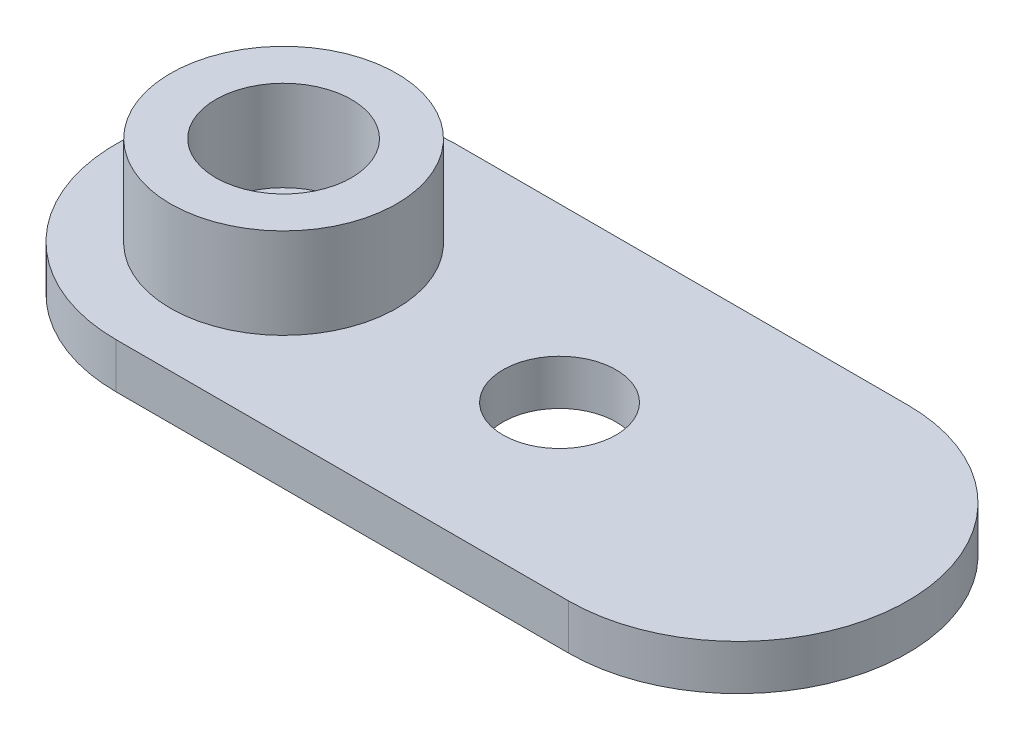
SolidWorks part; units mm, degrees
ref_plane "Front Plane" through (0, 0, 0) normal (0, 0, 1) x (1, 0, 0)
ref_plane "Top Plane" through (0, 0, 0) normal (0, 1, 0) x (1, 0, 0)
ref_plane "Right Plane" through (0, 0, 0) normal (1, 0, 0) x (0, 0, -1)
sketch "Sketch1" plane through (0, 0, 0) normal (0, 1, 0) x (1, 0, 0)
  line L0 (-7.5, 0.0986) -> (20, 0.0986) construction
  line L5 (-7.5, 0.0986) -> (27.5, 0.0986) construction
  line L6 (0, 7.5986) -> (0, -7.4014) construction
  line L7 (0, 7.5986) -> (20, 7.5986)
  line L8 (0, -7.4014) -> (20, -7.4014)
  arc A1 (20, -7.4014) -> (20, 7.5986) centre (20, 0.0986) ccw
  arc A2 (0, 7.5986) -> (0, -7.4014) centre (0, 0.0986) ccw
  point P0 (0, 0)
  point P8 (0, 0.0986)
extrude "Boss-Extrude1" add sketch "Sketch1" along normal blind 2
sketch "Sketch2" plane through (0, 2, 0) normal (0, 1, 0) x (1, 0, 0)
  circle A0 centre (0, 0) radius 5
  dimension "D1" = 10
extrude "Boss-Extrude3" add sketch "Sketch2" along normal blind 4
sketch "Sketch5" plane through (0, 6, 0) normal (0, 1, 0) x (1, 0, 0)
  circle A0 centre (0, 0) radius 3
extrude "Cut-Extrude1" cut sketch "Sketch5" against normal up to surface (4 mm away) contours A0 up to face at (0, 2, 5)
sketch "Sketch6" plane through (0, 2, 0) normal (0, 1, 0) x (1, 0, 0)
  circle A0 centre (0, 0) radius 1.5
extrude "Cut-Extrude2" cut sketch "Sketch6" against normal blind 2
sketch "Sketch7" plane through (0, 2, 0) normal (0, 1, 0) x (1, 0, 0)
  circle A0 centre (12.2, 0) radius 2.5
  dimension "D1" = 5
  dimension "D2" = 12.2
extrude "Cut-Extrude4" cut sketch "Sketch7" against normal through all contours A0
